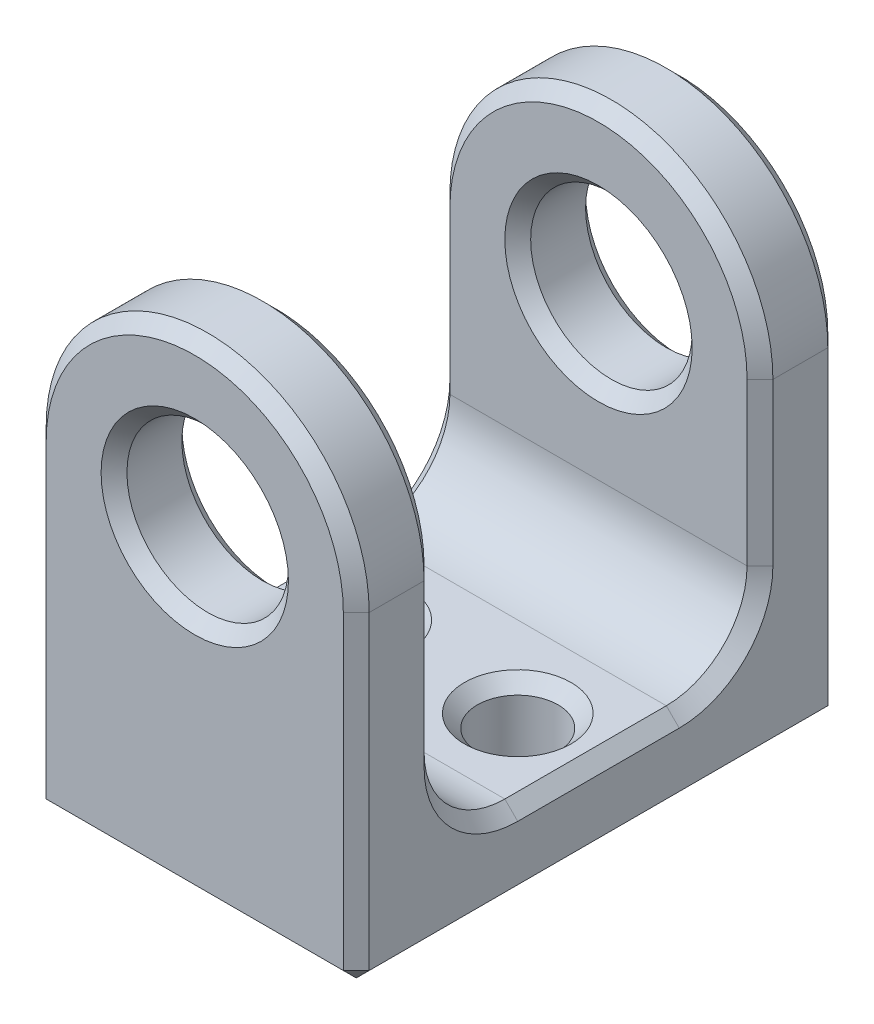
SolidWorks part; units mm, degrees
ref_plane "Front Plane" through (0, 0, 0) normal (0, 0, 1) x (1, 0, 0)
ref_plane "Top Plane" through (0, 0, 0) normal (0, 1, 0) x (1, 0, 0)
ref_plane "Right Plane" through (0, 0, 0) normal (1, 0, 0) x (0, 0, -1)
sketch "Sketch1" plane through (0, 0, 0) normal (0, 0, 1) x (1, 0, 0)
  line L2 (-6.35, 0) -> (-6.35, -12.7)
  line L3 (-6.35, -12.7) -> (6.35, -12.7)
  line L4 (6.35, 0) -> (6.35, -12.7)
  circle A0 centre (0, 0) radius 3.175
  arc A1 (6.35, 0) -> (-6.35, 0) centre (0, 0) ccw
  point P8 (0, -12.7)
  dimension "D1" = 6.35
  dimension "D4" = 12.7
  dimension "D2" = 12.7
extrude "Boss-Extrude1" add sketch "Sketch1" along normal mid plane 19.05
sketch "Sketch2" plane through (0, 0, 0) normal (1, 0, 0) x (0, 0, -1)
  line L1 (-6.35, 6.35) -> (6.35, 6.35)
  line L2 (-6.35, 6.35) -> (-6.35, -9.525)
  line L3 (-6.35, -9.525) -> (6.35, -9.525)
  line L4 (6.35, 6.35) -> (6.35, -9.525)
  line L5 (-9.525, -12.7) -> (9.525, -12.7) construction
  line L6 (9.525, 6.35) -> (-9.525, 6.35) construction
  point P6 (0, 6.35)
  dimension "D1" = 12.7
  dimension "D2" = 3.175
extrude "Cut-Extrude1" cut sketch "Sketch2" against normal through all both and the other way through all contours L1 L4 L3 L2
hole_wizard "1/8 (0.125) Diameter Hole1" positions "Sketch3" profile "Sketch4" hole size "1/8" standard "ANSI Inch" end condition through all
sketch "Sketch3" plane through (0, -9.525, 0) normal (0, 1, 0) x (1, 0, 0)
  line L0 (-3.175, 0) -> (3.175, 0) construction
  point P0 (-3.175, 0)
  point P2 (3.175, 0)
  dimension "D1" = 6.35
sketch "Sketch4" plane through (-3.175, -9.525, 0) normal (1, 0, 0) x (0, 0, 1)
  line L0 (0, 0) -> (0, 3.175)
  line L1 (0, 3.175) -> (1.5875, 3.175)
  line L2 (1.5875, 3.175) -> (1.5875, 0)
  line L5 (1.5875, 0) -> (0, 0)
  line L11 (0, -6.35) -> (0, 107.95) construction
  dimension "Thru Hole Dia." = 3.175
  dimension "Thru Hole Depth" = 3.175
ref_plane "Plane1" through (0, 6.35, 0) normal (0, 1, 0) x (1, 0, 0)
fillet "Fillet2" radius 3.175 2 edges at (0, -9.525, -6.35) (0, -9.525, 6.35)
chamfer "Chamfer1" distance 0.508 angle 45 30 edges at (-6.35, -6.35, 9.525) (3.175, 0, -9.525) (3.175, 0, 9.525) (0, -12.7, 9.525) (0, 6.35, 6.35) (-6.35, -3.175, 6.35) (0, -3.175, 6.35) (0, -3.175, -6.35) (6.35, -3.175, -6.35) (0, 6.35, -6.35) (-6.35, -3.175, -6.35) (6.35, -3.175, 6.35) (6.35, -6.35, 9.525) (0, -12.7, -9.525) (3.175, -9.525, 1.5875) (3.175, -12.7, 1.5875) (-6.35, -6.35, -9.525) (-3.175, -9.525, 1.5875) (-3.175, -12.7, 1.5875) (0, 6.35, -9.525) (-6.35, -9.525, 0) (6.35, -9.525, 0) (6.35, -6.35, -9.525) (6.35, -8.5951, -5.4201) (-6.35, -8.5951, -5.4201) (6.35, -8.5951, 5.4201) (-6.35, -8.5951, 5.4201) (0, 6.35, 9.525) (6.35, -12.7, 0) (-6.35, -12.7, 0)
